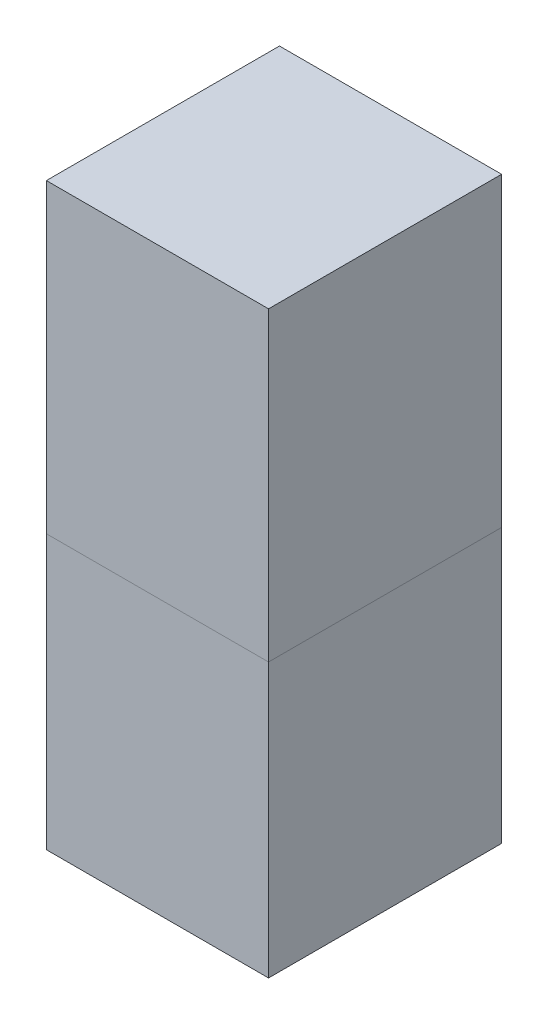
SolidWorks part; units mm, degrees
ref_plane "Front Plane" through (0, 0, 0) normal (0, 0, 1) x (1, 0, 0)
ref_plane "Top Plane" through (0, 0, 0) normal (0, 1, 0) x (1, 0, 0)
ref_plane "Right Plane" through (0, 0, 0) normal (1, 0, 0) x (0, 0, -1)
ref_plane "Plane1" through (0, -850, 0) normal (0, 1, 0) x (1, 0, 0)
sketch "Sketch3" plane through (0, -850, 0) normal (0, 1, 0) x (1, 0, 0)
  line L0 (345, 0) -> (344, 0) construction
  line L1 (-345, 361.95) -> (345, 361.95)
  line L2 (-345, 361.95) -> (-345, -361.95)
  line L3 (-345, -361.95) -> (345, -361.95)
  line L4 (345, 361.95) -> (345, -361.95)
  line L5 (0, -361.95) -> (0, 361.95) construction
  line L6 (-345, 0) -> (345, 0) construction
  line L7 (-345, 361.95) -> (345, 361.95)
  line L8 (-345, 361.95) -> (-345, -361.95)
  line L9 (-345, -361.95) -> (345, -361.95)
  line L10 (345, 361.95) -> (345, -361.95)
  line L11 (0, -361.95) -> (0, 361.95) construction
  line L12 (-345, 0) -> (345, 0) construction
  line L13 (0, 361.95) -> (0, 360.95) construction
  line L14 (-344, -360.95) -> (344, -360.95)
  line L15 (-344, 360.95) -> (-344, -360.95)
  line L16 (-344, 360.95) -> (344, 360.95)
  line L17 (344, 360.95) -> (344, -360.95)
  point P0 (0, 0)
  point P4 (0, 0)
  dimension "D1" = 723.9
  dimension "D2" = 690
  dimension "D3" = 1
  dimension "D4" = 1
  dimension "D5" = 1
extrude "Boss-Extrude4" add sketch "Sketch3" along normal blind 850 contours L4 L1 L2 L3 L16 L17 L14 L15
sketch "Sketch4" plane through (0, -850, 0) normal (0, 1, 0) x (1, 0, 0)
  line L1 (-344, -360.95) -> (344, -360.95)
  line L2 (-344, -360.95) -> (-344, 360.95)
  line L3 (-344, 360.95) -> (344, 360.95)
  line L4 (344, -360.95) -> (344, 360.95)
  dimension "D1" = 721.9
  dimension "D2" = 688
extrude "Boss-Extrude5" add sketch "Sketch4" along normal blind 1
sketch "Sketch8" plane through (0, 0, 0) normal (0, 1, 0) x (1, 0, 0)
  line L0 (-345, 361.95) -> (345, 361.95)
  line L2 (-345, -361.95) -> (345, -361.95)
  line L3 (-345, -361.95) -> (-345, 361.95)
  line L4 (-345, 361.95) -> (345, 361.95)
  line L5 (345, -361.95) -> (345, 361.95)
  line L6 (-344, 360.95) -> (344, 360.95)
  line L7 (-344, 360.95) -> (-344, -360.95)
  line L8 (-344, -360.95) -> (344, -360.95)
  line L9 (344, 360.95) -> (344, -360.95)
  dimension "D1" = 723.9
  dimension "D2" = 690
  dimension "D3" = 721.9
  dimension "D4" = 688
extrude "Boss-Extrude7" add sketch "Sketch8" against normal blind 0.99 separate body contours L9 L6 L7 L8 | L2 L5 L0 L3 L6 L9 L8 L7
sketch "Sketch10" plane through (0, 0, 0) normal (0, 1, 0) x (1, 0, 0)
  line L12 (-344, -360.95) -> (344, -360.95)
  line L13 (-344, -360.95) -> (-344, 360.95)
  line L14 (-344, 360.95) -> (344, 360.95)
  line L15 (-343.9, -360.85) -> (343.9, -360.85)
  line L16 (343.9, -360.85) -> (343.9, 360.85)
  line L17 (343.9, 360.85) -> (-343.9, 360.85)
  line L18 (-343.9, 360.85) -> (-343.9, -360.85)
  line L19 (-343.9, -360.85) -> (343.9, -360.85)
  line L20 (343.9, -360.85) -> (343.9, 360.85)
  line L21 (343.9, 360.85) -> (-343.9, 360.85)
  line L22 (-343.9, 360.85) -> (-343.9, -360.85)
  line L23 (344, -360.95) -> (344, 360.95)
  dimension "D2" = 721.9
  dimension "D3" = 688
  dimension "D1" = 0.1
extrude "Boss-Extrude8" add sketch "Sketch10" against normal blind 1.5
ref_plane "Plane2" through (0, 0, 361.95) normal (0, 0, 1) x (1, 0, 0)
sketch "Sketch12" plane through (0, 0, 361.95) normal (0, 0, 1) x (1, 0, 0)
  line L0 (0, -850) -> (0, -545.2) construction
  line L1 (-345, -850) -> (345, -850) construction
  line L2 (0, -545.2) -> (0, -535.2) construction
  line L3 (-345, -425) -> (-305, -425) construction
  line L4 (-345, 0) -> (-345, -850) construction
  line L5 (345, -425) -> (305, -425) construction
  line L6 (345, 0) -> (345, -850) construction
  line L7 (0, 0) -> (0, -40) construction
  line L8 (0, -40) -> (0, -50) construction
  line L9 (-345, -40) -> (345, -40)
  line L10 (0, -50) -> (0, -80) construction
  line L11 (0, -535.2) -> (0, -505.2) construction
  line L12 (-305, -425) -> (-295, -425) construction
  line L13 (305, -425) -> (295, -425) construction
  line L14 (0, -505.2) -> (0, -495.2) construction
  line L15 (0, -80) -> (0, -90) construction
  line L16 (-345, -545.2) -> (345, -545.2)
  line L17 (-265, -90) -> (265, -90)
  line L18 (-295, -120) -> (-295, -465.2)
  line L19 (-265, -495.2) -> (265, -495.2)
  line L20 (295, -120) -> (295, -465.2)
  line L21 (-295, -292.6) -> (-280, -292.6) construction
  line L22 (-345, -505.2) -> (345, -505.2)
  line L23 (-345, -505.2) -> (-345, -535.2)
  line L24 (-345, -535.2) -> (345, -535.2)
  line L25 (345, -505.2) -> (345, -535.2)
  line L26 (-345, -545.2) -> (345, -545.2)
  line L27 (-345, -545.2) -> (-345, -850)
  line L28 (-345, -850) -> (345, -850)
  line L29 (345, -545.2) -> (345, -850)
  line L30 (-280, -292.6) -> (-280, -252.6) construction
  line L31 (-274, -262.6) -> (-274, -322.6)
  line L32 (-270, -252.6) -> (-250, -252.6)
  line L33 (-280, -262.6) -> (-280, -322.6)
  line L34 (-270, -332.6) -> (-250, -332.6)
  line L35 (-250, -252.6) -> (-250, -332.6)
  line L36 (-270, -326.6) -> (-256, -326.6)
  line L37 (-256, -258.6) -> (-256, -326.6)
  line L38 (-270, -258.6) -> (-256, -258.6)
  line L39 (-345, -50) -> (345, -50)
  arc A0 (-295, -465.2) -> (-265, -495.2) centre (-265, -465.2) ccw
  arc A1 (265, -495.2) -> (295, -465.2) centre (265, -465.2) ccw
  arc A2 (265, -90) -> (295, -120) centre (265, -120) cw
  arc A3 (-265, -90) -> (-295, -120) centre (-265, -120) ccw
  arc A4 (-280, -322.6) -> (-270, -332.6) centre (-270, -322.6) ccw
  arc A5 (-280, -262.6) -> (-270, -252.6) centre (-270, -262.6) cw
  arc A6 (-274, -322.6) -> (-270, -326.6) centre (-270, -322.6) ccw
  arc A7 (-274, -262.6) -> (-270, -258.6) centre (-270, -262.6) cw
  point P42 (-295, -495.2)
  point P47 (295, -90)
  point P50 (-295, -90)
  point P59 (-280, -332.6)
  dimension "D9" = 30
  dimension "D12" = 10
  dimension "D1" = 10
  dimension "D2" = 30
  dimension "D3" = 405.2
  dimension "D4" = 590
  dimension "D5" = 30
  dimension "D6" = 690
  dimension "D7" = 304.8
  dimension "D8" = 690
  dimension "D10" = 80
  dimension "D11" = 30
  dimension "D13" = 6
ref_plane "Plane3" through (-345, 0, 0) normal (1, 0, 0) x (0, 0, -1)
sketch "Sketch13" plane through (-345, 0, 0) normal (1, 0, 0) x (0, 0, -1)
  line L0 (0, 0) -> (0, -40) construction
  line L1 (361.95, -40) -> (-361.95, -40)
  line L2 (361.95, 0) -> (361.95, -850) construction
  line L3 (-361.95, 0) -> (-361.95, -40) construction
  line L4 (-361.95, -40) -> (-361.95, -50) construction
  line L5 (0, -40) -> (0, -50) construction
  line L6 (-361.95, -425) -> (-321.95, -425) construction
  line L7 (-361.95, -120) -> (-361.95, -465.2) construction
  line L8 (-321.95, -425) -> (-311.95, -425) construction
  line L10 (361.95, -50) -> (-361.95, -50)
  line L11 (-361.95, -50) -> (-361.95, -80) construction
  line L12 (-361.95, -535.2) -> (-321.95, -535.2)
  line L14 (-321.95, -545.2) -> (-321.95, -850)
  line L15 (-321.95, -545.2) -> (-361.95, -545.2)
  line L16 (-321.95, -535.2) -> (-321.95, -50)
  line L17 (361.95, -850) -> (-361.95, -850) construction
  line L18 (-311.95, -850) -> (-311.95, -50)
  dimension "D1" = 10
  dimension "D2" = 304.8
  dimension "D3" = 10
  dimension "D4" = 485.2
ref_plane "Plane4" through (345, 0, 0) normal (1, 0, 0) x (0, 0, -1)
sketch "Sketch14" plane through (345, 0, 0) normal (1, 0, 0) x (0, 0, -1)
  line L0 (0, 0) -> (0, -40) construction
  line L1 (-361.95, -425) -> (-321.95, -425) construction
  line L2 (-361.95, 0) -> (-361.95, -850) construction
  line L3 (-361.95, -40) -> (361.95, -40)
  line L4 (-321.95, -425) -> (-311.95, -425) construction
  line L5 (0, -40) -> (0, -50) construction
  line L6 (-361.95, -50) -> (361.95, -50)
  line L7 (361.95, 0) -> (361.95, -850) construction
  line L8 (-321.95, -50) -> (-321.95, -535.2)
  line L9 (-321.95, -535.2) -> (-361.95, -535.2)
  line L10 (-361.95, -545.2) -> (-321.95, -545.2)
  line L11 (-321.95, -545.2) -> (-321.95, -850)
  line L12 (-311.95, -850) -> (-311.95, -50)
ref_plane "Plane5" through (0, 0, -361.95) normal (0, 0, 1) x (1, 0, 0)
sketch "Sketch15" plane through (0, 0, -361.95) normal (0, 0, 1) x (1, 0, 0)
  line L0 (345, -40) -> (-345, -40)
  line L1 (345, -50) -> (-345, -50)
  line L2 (-345, -50) -> (345, -50) construction
  dimension "D1" = 690
move or copy body "Body-Move/Copy1" bodies to move or copy 108 copy yes number of copies 1 translate (0, -850, 0)
sketch "Sketch16" plane through (0, 0, 0) normal (0, 1, 0) x (1, 0, 0)
  line L1 (-345, 361.95) -> (345, 361.95)
  line L2 (-345, 361.95) -> (-345, -361.95)
  line L3 (-345, -361.95) -> (345, -361.95)
  line L4 (345, 361.95) -> (345, -361.95)
  dimension "D1" = 723.9
  dimension "D2" = 690
extrude "Boss-Extrude9" add sketch "Sketch16" along normal blind 100
